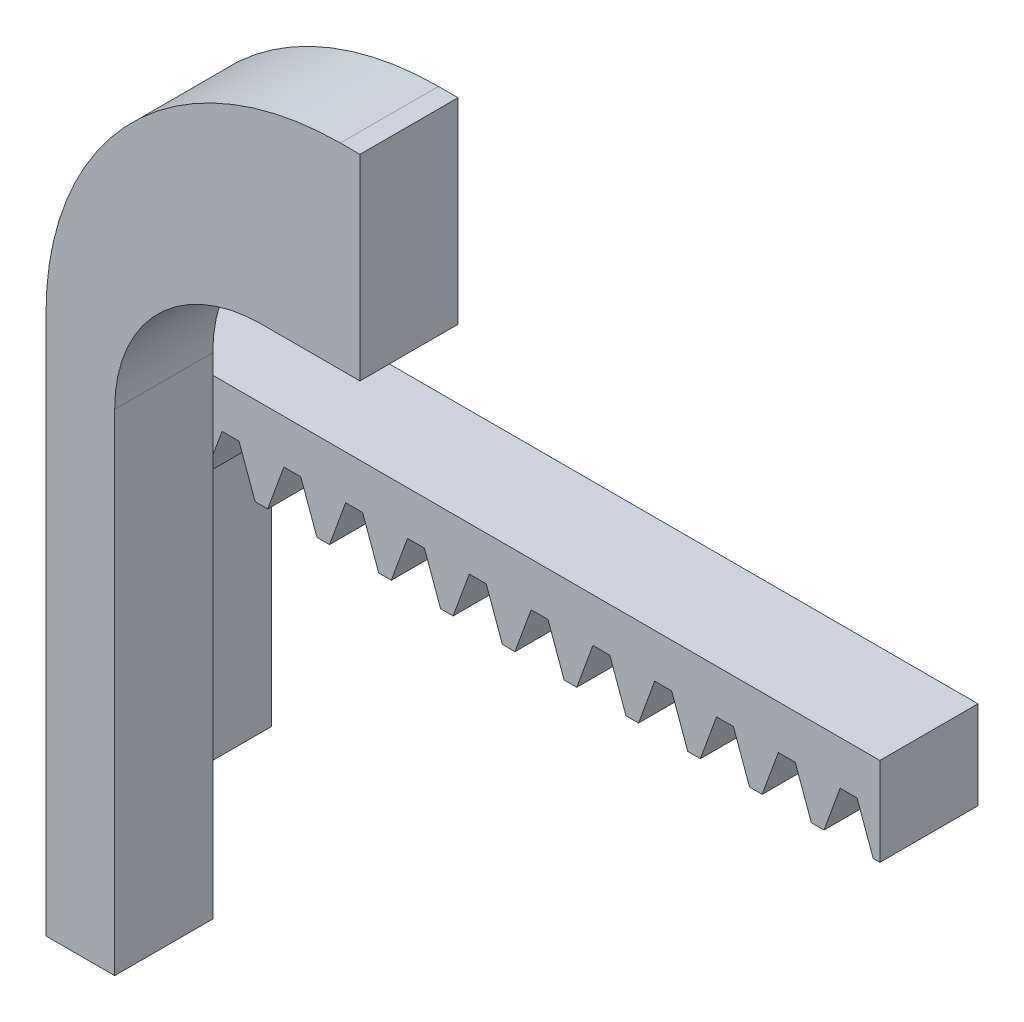
SolidWorks part; units mm, degrees
ref_plane "Ebene vorne" through (0, 0, 0) normal (0, 0, 1) x (1, 0, 0)
ref_plane "Ebene oben" through (0, 0, 0) normal (0, 1, 0) x (1, 0, 0)
ref_plane "Ebene rechts" through (0, 0, 0) normal (1, 0, 0) x (0, 0, -1)
sketch "Sketch1" plane through (0, 0, 0) normal (0, 0, 1) x (1, 0, 0)
  line L1 (7, 0) -> (0, 0)
  line L4 (0, 0) -> (0, 47.7)
  line L6 (7, 50) -> (7, 0)
  line L7 (32, 85) -> (32, 65)
  line L8 (32, 65) -> (22, 65)
  line L9 (32, 85) -> (30, 85)
  line L10 (0, 47.7) -> (0, 55)
  arc A0 (22, 65) -> (7, 50) centre (22, 50) ccw
  arc A2 (30, 85) -> (0, 55) centre (30, 55) ccw
  dimension "D6" = 30
  dimension "D8" = 30
  dimension "D1" = 20
  dimension "D2" = 85
  dimension "D3" = 47.7
  dimension "D4" = 7
  dimension "D5" = 32
  dimension "D7" = 50
  dimension "D9" = 10
extrude "Boss-Extrude1" add sketch "Sketch1" along normal blind 10
sketch "Skizze2" plane through (0, 0, 0) normal (0, 0, -1) x (-1, 0, 0)
  line L0 (0, 55) -> (0, 0) construction
  line L1 (0, 48) -> (-75, 48)
  line L2 (0, 48) -> (0, 39)
  line L3 (0, 39) -> (-75, 39)
  line L4 (-75, 48) -> (-75, 39)
  line L5 (0, 0) -> (-7, 0) construction
  dimension "D1" = 75
  dimension "D2" = 9
  dimension "D3" = 48
extrude "Aufsatz-Linear austragen1" add sketch "Skizze2" along normal blind 10
sketch "Skizze3" plane through (0, 0, -10) normal (0, 0, -1) x (-1, 0, 0)
  line L168 (-3.3709, 43.5254) -> (-1.6471, 43.5254)
  line L169 (-5.018, 39) -> (-3.3709, 43.5254)
  line L170 (-5.018, 39) -> (0, 39)
  line L171 (0, 39) -> (-1.6471, 43.5254)
  line L172 (-1.6904, 43.6444) -> (-3.3275, 43.6444) construction
  line L217 (-9.6709, 43.5254) -> (-7.9471, 43.5254)
  line L218 (-6.3, 39) -> (-7.9471, 43.5254)
  line L219 (-11.318, 39) -> (-6.3, 39)
  line L220 (-11.318, 39) -> (-9.6709, 43.5254)
  line L221 (-15.9709, 43.5254) -> (-14.2471, 43.5254)
  line L222 (-12.6, 39) -> (-14.2471, 43.5254)
  line L223 (-17.618, 39) -> (-12.6, 39)
  line L224 (-17.618, 39) -> (-15.9709, 43.5254)
  line L225 (-22.2709, 43.5254) -> (-20.5471, 43.5254)
  line L226 (-18.9, 39) -> (-20.5471, 43.5254)
  line L227 (-23.918, 39) -> (-18.9, 39)
  line L228 (-23.918, 39) -> (-22.2709, 43.5254)
  line L229 (-28.5709, 43.5254) -> (-26.8471, 43.5254)
  line L230 (-25.2, 39) -> (-26.8471, 43.5254)
  line L231 (-30.218, 39) -> (-25.2, 39)
  line L232 (-30.218, 39) -> (-28.5709, 43.5254)
  line L233 (-34.8709, 43.5254) -> (-33.1471, 43.5254)
  line L234 (-31.5, 39) -> (-33.1471, 43.5254)
  line L235 (-36.518, 39) -> (-31.5, 39)
  line L236 (-36.518, 39) -> (-34.8709, 43.5254)
  line L237 (-41.1709, 43.5254) -> (-39.4471, 43.5254)
  line L238 (-37.8, 39) -> (-39.4471, 43.5254)
  line L239 (-42.818, 39) -> (-37.8, 39)
  line L240 (-42.818, 39) -> (-41.1709, 43.5254)
  line L241 (-47.4709, 43.5254) -> (-45.7471, 43.5254)
  line L242 (-44.1, 39) -> (-45.7471, 43.5254)
  line L243 (-49.118, 39) -> (-44.1, 39)
  line L244 (-49.118, 39) -> (-47.4709, 43.5254)
  line L245 (-53.7709, 43.5254) -> (-52.0471, 43.5254)
  line L246 (-50.4, 39) -> (-52.0471, 43.5254)
  line L247 (-55.418, 39) -> (-50.4, 39)
  line L248 (-55.418, 39) -> (-53.7709, 43.5254)
  line L249 (-60.0709, 43.5254) -> (-58.3471, 43.5254)
  line L250 (-56.7, 39) -> (-58.3471, 43.5254)
  line L251 (-61.718, 39) -> (-56.7, 39)
  line L252 (-61.718, 39) -> (-60.0709, 43.5254)
  line L253 (-66.3709, 43.5254) -> (-64.6471, 43.5254)
  line L254 (-63, 39) -> (-64.6471, 43.5254)
  line L255 (-68.018, 39) -> (-63, 39)
  line L256 (-68.018, 39) -> (-66.3709, 43.5254)
  line L257 (-72.6709, 43.5254) -> (-70.9471, 43.5254)
  line L258 (-69.3, 39) -> (-70.9471, 43.5254)
  line L259 (-74.318, 39) -> (-69.3, 39)
  line L260 (-74.318, 39) -> (-72.6709, 43.5254)
  dimension "D1" = 5.018
  dimension "D2" = 1.7237
extrude "Schnitt-Linear austragen2" cut sketch "Skizze3" against normal blind 10
sketch "Skizze4" plane through (0, 0, 0) normal (-1, 0, 0) x (0, 0, 1)
  line L1 (10, 0) -> (-10, 0)
  line L2 (10, 0) -> (10, 48)
  line L3 (10, 48) -> (-10, 48)
  line L4 (-10, 0) -> (-10, 48)
  line L5 (-10, 39) -> (-10, 48) construction
  line L6 (-10, 48) -> (0, 48) construction
extrude "Aufsatz-Linear austragen2" add sketch "Skizze4" against normal blind 3
sketch "Skizze5" plane through (3, 0, 0) normal (1, 0, 0) x (0, 0, -1)
  line L0 (0, 43.5254) -> (0, 0) construction
  line L1 (10, 0) -> (0, 0)
  line L2 (10, 0) -> (10, 10)
  line L3 (10, 10) -> (0, 10)
  line L4 (0, 0) -> (0, 10)
  dimension "D1" = 10
extrude "Schnitt-Linear austragen3" cut sketch "Skizze5" against normal blind 10
